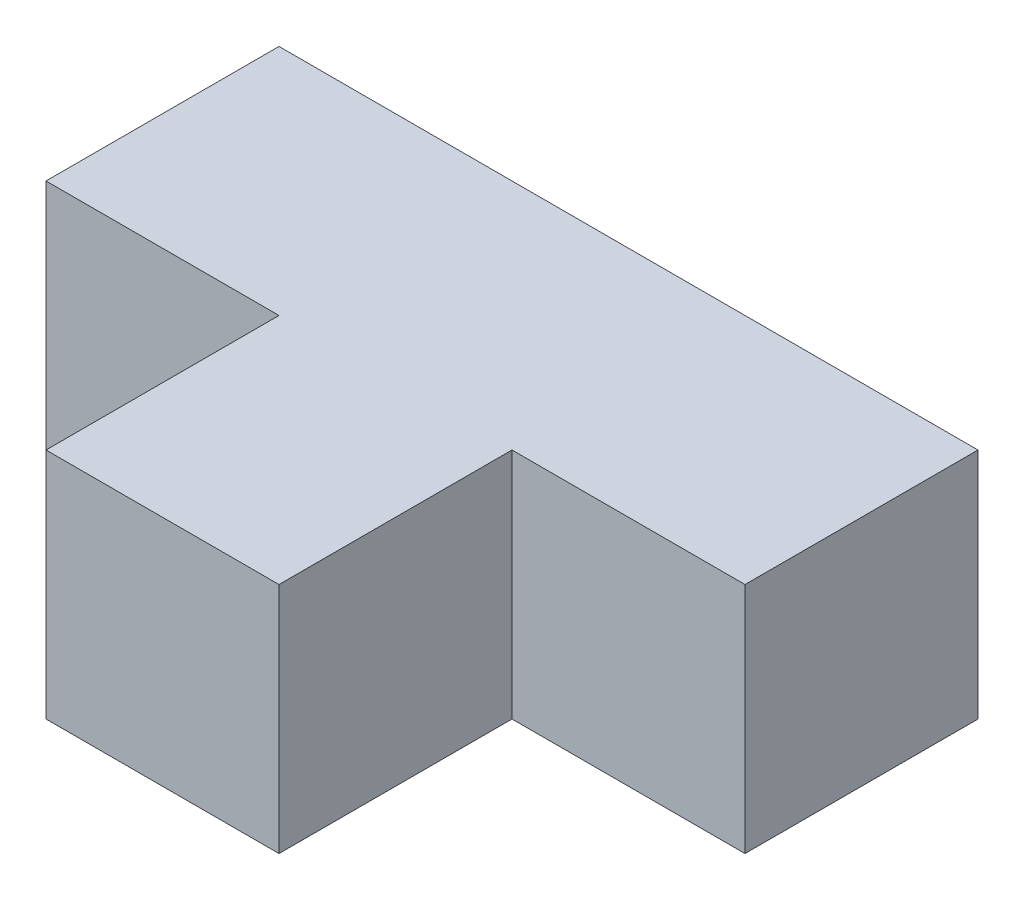
SolidWorks part; units mm, degrees
ref_plane "Front Plane" through (0, 0, 0) normal (0, 0, 1) x (1, 0, 0)
ref_plane "Top Plane" through (0, 0, 0) normal (0, 1, 0) x (1, 0, 0)
ref_plane "Right Plane" through (0, 0, 0) normal (1, 0, 0) x (0, 0, -1)
sketch "Sketch1" plane through (0, 0, 0) normal (0, 1, 0) x (1, 0, 0)
  line L1 (-38.1, -25.4) -> (38.1, -25.4)
  line L2 (-38.1, -25.4) -> (-38.1, 25.4)
  line L3 (-38.1, 25.4) -> (38.1, 25.4)
  line L4 (38.1, -25.4) -> (38.1, 25.4)
  line L5 (-38.1, -25.4) -> (38.1, 25.4) construction
  line L6 (-38.1, 25.4) -> (38.1, -25.4) construction
  point P0 (0, 0)
  dimension "D1" = 76.2
  dimension "D2" = 50.8
extrude "Boss-Extrude1" add sketch "Sketch1" along normal blind 25.4
sketch "Sketch2" plane through (0, 25.4, 0) normal (0, 1, 0) x (1, 0, 0)
  line L1 (-38.1, -25.4) -> (-12.7, -25.4)
  line L2 (-38.1, -25.4) -> (-38.1, 0)
  line L3 (-38.1, 0) -> (-12.7, 0)
  line L4 (-12.7, -25.4) -> (-12.7, 0)
  dimension "D1" = 25.4
  dimension "D2" = 25.4
extrude "Cut-Extrude1" cut sketch "Sketch2" against normal through all
mirror "Mirror1" about plane through (0, 0, 0) normal (1, 0, 0) of "Cut-Extrude1"
